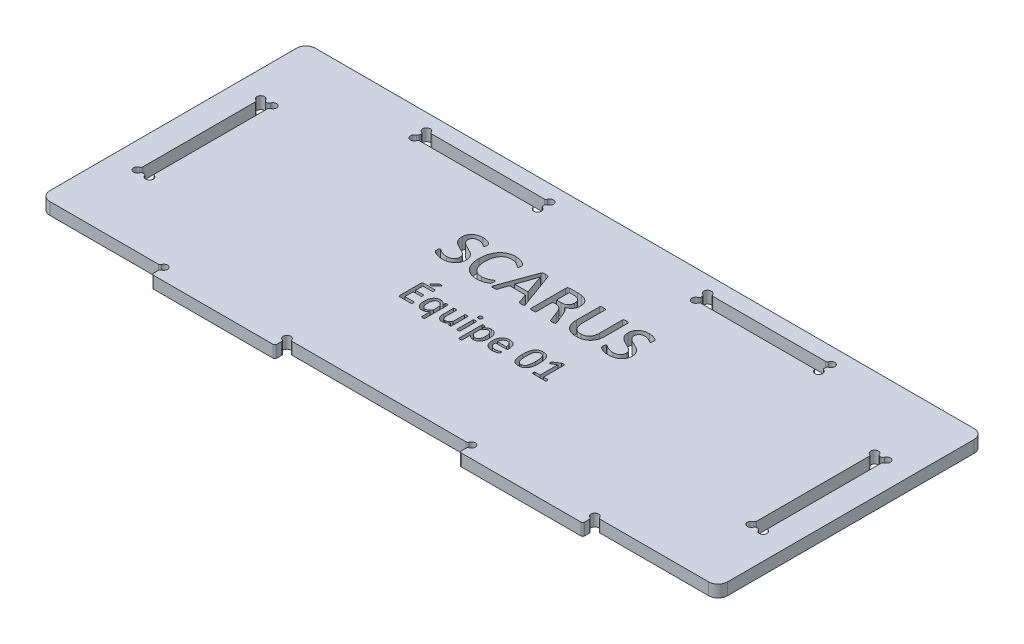
SolidWorks part; units mm, degrees
material "Pine"
ref_plane "Front Plane" through (0, 0, 0) normal (0, 0, 1) x (1, 0, 0)
ref_plane "Top Plane" through (0, 0, 0) normal (0, 1, 0) x (1, 0, 0)
ref_plane "Right Plane" through (0, 0, 0) normal (1, 0, 0) x (0, 0, -1)
sketch "Sketch1" plane through (0, 0, 0) normal (0, 1, 0) x (1, 0, 0)
  line L1 (-178.65, 70) -> (178.65, 70)
  line L2 (-178.65, 70) -> (-178.65, -70)
  line L3 (-178.65, -70) -> (178.65, -70)
  line L4 (178.65, 70) -> (178.65, -70)
  line L5 (-178.65, 70) -> (178.65, -70) construction
  line L6 (-178.65, -70) -> (178.65, 70) construction
  point P0 (0, 0)
  dimension "D1" = 357.3
  dimension "D2" = 140
extrude "Boss-Extrude1" add sketch "Sketch1" along normal blind 6.35
sketch "Sketch10" plane through (0, 6.35, 0) normal (0, 1, 0) x (1, 0, 0)
  line L1 (-165, 32.5) -> (-158.65, 32.5)
  line L2 (-165, 32.5) -> (-165, -32.5)
  line L3 (-165, -32.5) -> (-158.65, -32.5)
  line L4 (-158.65, 32.5) -> (-158.65, -32.5)
  line L5 (-158.3381, 32.5) -> (-158.3381, 70) construction
  line L7 (178.65, 70) -> (-178.65, 70) construction
  line L9 (-155.0312, -32.5) -> (-155.0312, -70) construction
  line L10 (-178.65, -70) -> (178.65, -70) construction
  line L11 (-178.65, 70) -> (-178.65, -70) construction
  dimension "D1" = 13.65
  dimension "D2" = 65
  dimension "D3" = 6.35
extrude "Cut-Extrude1" cut sketch "Sketch10" against normal up to surface (6.35 mm away) up to face at (0, 0, 0)
sketch "Sketch11" plane through (0, 6.35, 0) normal (0, 1, 0) x (1, 0, 0)
  circle A0 centre (-158.65, 32.5) radius 2
  circle A1 centre (-165, 32.5) radius 2
  circle A2 centre (-165, -32.5) radius 2
  circle A3 centre (-158.65, -32.5) radius 2
  dimension "D1" = 4
extrude "Cut-Extrude2" cut sketch "Sketch11" against normal up to surface (6.35 mm away) up to face at (-161.825, 0, 0)
fillet "Fillet1" radius 1 8 edges at (-165, 3.175, 30.5) (-163, 3.175, 32.5) (-160.65, 3.175, 32.5) (-158.65, 3.175, 30.5) (-165, 3.175, -30.5) (-158.65, 3.175, -30.5) (-160.65, 3.175, -32.5) (-163, 3.175, -32.5)
mirror "Mirror1" about plane through (0, 0, 0) normal (1, 0, 0) of "Cut-Extrude1", "Cut-Extrude2", "Fillet1"
sketch "Sketch12" plane through (0, 6.35, 0) normal (0, 1, 0) x (1, 0, 0)
  line L0 (-178.65, -70) -> (178.65, -70) construction
  line L1 (-113.65, -70) -> (-48.65, -70)
  line L2 (-113.65, -70) -> (-113.65, -76.35)
  line L3 (-113.65, -76.35) -> (-48.65, -76.35)
  line L4 (-48.65, -70) -> (-48.65, -76.35)
  line L5 (-178.65, 70) -> (-178.65, -70) construction
  dimension "D1" = 65
  dimension "D2" = 65
  dimension "D3" = 6.35
extrude "Boss-Extrude2" add sketch "Sketch12" against normal up to surface (6.35 mm away) up to face at (161.825, 0, 0)
sketch "Sketch13" plane through (0, 6.35, 0) normal (0, 1, 0) x (1, 0, 0)
  circle A0 centre (-113.65, -70) radius 2
  circle A1 centre (-48.65, -70) radius 2
  dimension "D1" = 4
extrude "Cut-Extrude3" cut sketch "Sketch13" against normal up to surface (6.35 mm away) up to face at (161.825, 0, 0)
fillet "Fillet2" radius 1 6 edges at (-46.65, 3.175, 70) (-48.65, 3.175, 72) (-48.65, 3.175, 76.35) (-113.65, 3.175, 76.35) (-113.65, 3.175, 72) (-115.65, 3.175, 70)
mirror "Mirror2" about plane through (0, 0, 0) normal (1, 0, 0) of "Boss-Extrude2", "Cut-Extrude3", "Fillet2"
fillet "Fillet3" radius 5 4 edges at (178.65, 3.175, -70) (178.65, 3.175, 70) (-178.65, 3.175, 70) (-178.65, 3.175, -70)
sketch "Sketch14" plane through (0, 6.35, 0) normal (0, 1, 0) x (1, 0, 0)
  text T0 "SCARUS" font "Calibri" height 20
  text T1 "Équipe 01" font "Calibri" height 12.5
extrude "Cut-Extrude4" cut sketch "Sketch14" against normal up to surface (6.35 mm away) up to face at (0, 0, 54.2468)
sketch "Sketch15" plane through (0, 6.35, 0) normal (0, 1, 0) x (1, 0, 0)
  line L0 (178.65, -65) -> (178.65, 65) construction
  line L1 (41.65, 61.52) -> (106.65, 61.52)
  line L2 (41.65, 61.52) -> (41.65, 55.17)
  line L3 (41.65, 55.17) -> (106.65, 55.17)
  line L4 (106.65, 61.52) -> (106.65, 55.17)
  line L5 (173.65, 70) -> (-173.65, 70) construction
  dimension "D1" = 65
  dimension "D2" = 72
  dimension "D3" = 6.35
  dimension "D4" = 8.48
extrude "Cut-Extrude5" cut sketch "Sketch15" against normal up to surface (6.35 mm away) up to face at (-34.5854, 0, 15.042)
sketch "Sketch16" plane through (0, 6.35, 0) normal (0, 1, 0) x (1, 0, 0)
  line L0 (41.65, 55.17) -> (106.65, 55.17) construction
  circle A0 centre (41.65, 61.52) radius 2
  circle A1 centre (41.65, 55.17) radius 2
  circle A2 centre (106.65, 61.52) radius 2
  circle A3 centre (106.65, 55.17) radius 2
  dimension "D1" = 4
extrude "Cut-Extrude6" cut sketch "Sketch16" against normal up to surface (6.35 mm away) up to face at (74.15, 0, -58.345)
fillet "Fillet4" radius 1 8 edges at (104.65, 3.175, -55.17) (106.65, 3.175, -57.17) (106.65, 3.175, -59.52) (104.65, 3.175, -61.52) (43.65, 3.175, -55.17) (41.65, 3.175, -57.17) (43.65, 3.175, -61.52) (41.65, 3.175, -59.52)
mirror "Mirror3" about plane through (0, 0, 0) normal (1, 0, 0) of "Cut-Extrude5", "Cut-Extrude6", "Fillet4"
